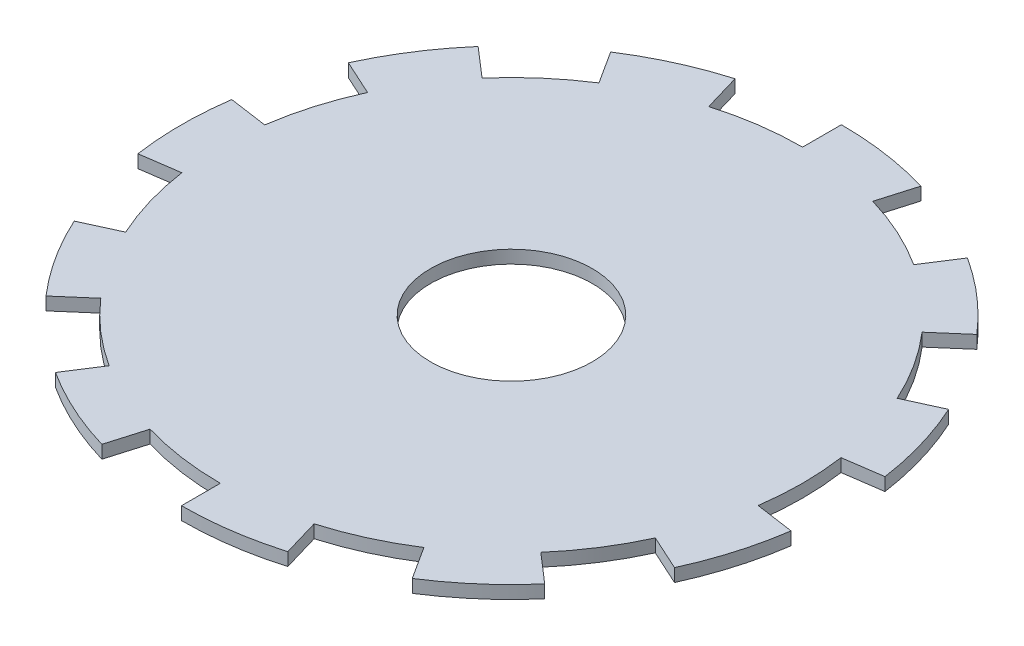
SolidWorks part; units mm, degrees
ref_plane "Front Plane" through (0, 0, 0) normal (0, 0, 1) x (1, 0, 0)
ref_plane "Top Plane" through (0, 0, 0) normal (0, 1, 0) x (1, 0, 0)
ref_plane "Right Plane" through (0, 0, 0) normal (1, 0, 0) x (0, 0, -1)
sketch "Sketch1" plane through (0, 0, 0) normal (0, 1, 0) x (1, 0, 0)
  circle A0 centre (0, 0) radius 45
  dimension "D1" = 90
extrude "Boss-Extrude1" add sketch "Sketch1" along normal blind 2
sketch "Sketch2" plane through (0, 0, 0) normal (0, 1, 0) x (1, 0, 0)
  line L0 (0, 0) -> (-51, 0)
  line L1 (-50.4811, -7.2565) -> (0, 0)
  circle A0 centre (0, 0) radius 45 construction
  arc A1 (-51, 0) -> (-50.4811, -7.2565) centre (0, 0) ccw
  dimension "D1" = 51
  dimension "D2" = 8.18
extrude "Boss-Extrude2" add sketch "Sketch2" along normal up to surface (2 mm away) up to face at (0, 2, 45)
mirror "Mirror1" about plane through (0, 0, 0) normal (0, 0, 1) of "Boss-Extrude2"
pattern_circular "CirPattern1" count 11 over 360 about axis through (0, 0, 0) along (0, 1, 0) of "Mirror1", "Boss-Extrude2"
sketch "Sketch3" plane through (0, 2, 0) normal (0, 1, 0) x (1, 0, 0)
  circle A0 centre (0, 0) radius 12.5
  dimension "D1" = 25
extrude "Cut-Extrude1" cut sketch "Sketch3" against normal blind 2
